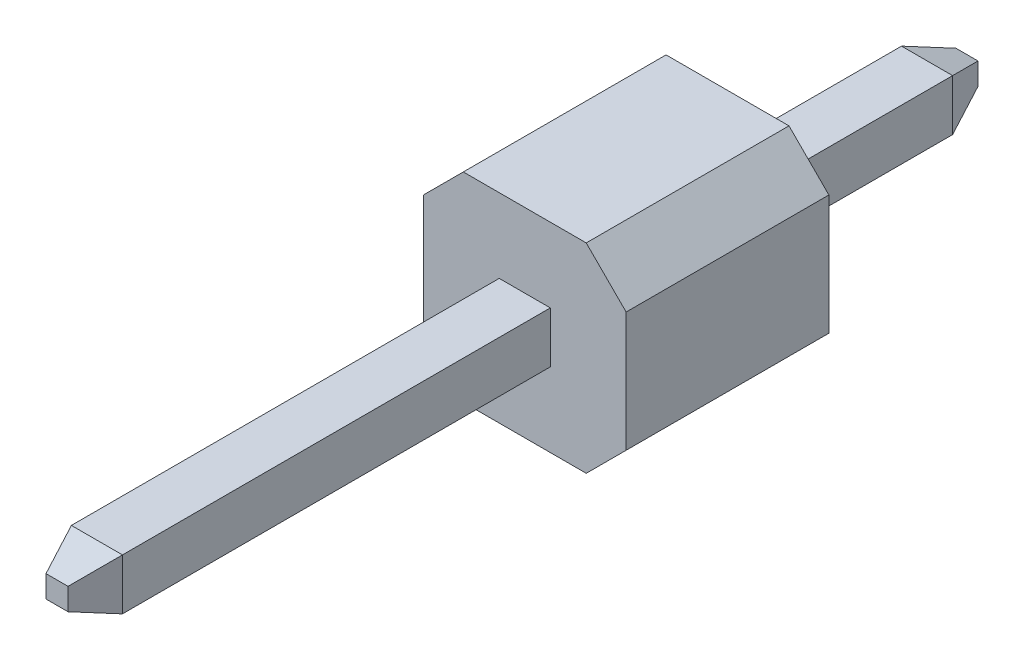
SolidWorks part; units mm, degrees
ref_plane "Front Plane" through (0, 0, 0) normal (0, 0, 1) x (1, 0, 0)
ref_plane "Top Plane" through (0, 0, 0) normal (0, 1, 0) x (1, 0, 0)
ref_plane "Right Plane" through (0, 0, 0) normal (1, 0, 0) x (0, 0, -1)
sketch "Sketch1" plane through (0, 0, 0) normal (0, 0, 1) x (1, 0, 0)
  line L0 (0, 0.32) -> (0, -0.32) construction
  line L1 (-0.32, 0.32) -> (0.32, 0.32)
  line L2 (-0.32, 0.32) -> (-0.32, -0.32)
  line L3 (-0.32, -0.32) -> (0.32, -0.32)
  line L4 (0.32, 0.32) -> (0.32, -0.32)
  point P6 (0, 0)
  point P7 (0, 0)
  dimension "D1" = 0.64
extrude "Boss-Extrude1" add sketch "Sketch1" along normal blind 8.4
sketch "Sketch2" plane through (0, 0, 0) normal (0, 0, -1) x (-1, 0, 0)
  line L1 (0.32, 0.32) -> (-0.32, 0.32)
  line L2 (0.32, 0.32) -> (0.32, -0.32)
  line L3 (0.32, -0.32) -> (-0.32, -0.32)
  line L4 (-0.32, 0.32) -> (-0.32, -0.32)
extrude "Boss-Extrude2" add sketch "Sketch2" along normal blind 3
chamfer "Chamfer1" distance 0.5 angle 20 8 edges at (0.32, 0, 8.4) (0, 0.32, 8.4) (-0.32, 0, 8.4) (0, -0.32, 8.4) (0, 0.32, -3) (-0.32, 0, -3) (0.32, 0, -3) (0, -0.32, -3)
sketch "Sketch3" plane through (0, 0, 0) normal (0, 0, 1) x (1, 0, 0)
  line L0 (0, 1.25) -> (0, -1.25) construction
  line L1 (-1.27, 1.25) -> (1.27, 1.25)
  line L2 (-1.27, 1.25) -> (-1.27, -1.25)
  line L3 (-1.27, -1.25) -> (1.27, -1.25)
  line L4 (1.27, 1.25) -> (1.27, -1.25)
  point P6 (0, 0)
  point P7 (0, 0)
  dimension "D1" = 2.5
  dimension "D2" = 2.54
extrude "Boss-Extrude3" add sketch "Sketch3" along normal blind 2.54
chamfer "Chamfer2" distance 0.5 angle 45 4 edges at (1.27, 1.25, 1.27) (1.27, -1.25, 1.27) (-1.27, 1.25, 1.27) (-1.27, -1.25, 1.27)
sketch "Sketch5" plane through (0, 0, 0) normal (0, 0, -1) x (-1, 0, 0)
  circle A0 centre (0, 0) radius 0.5
